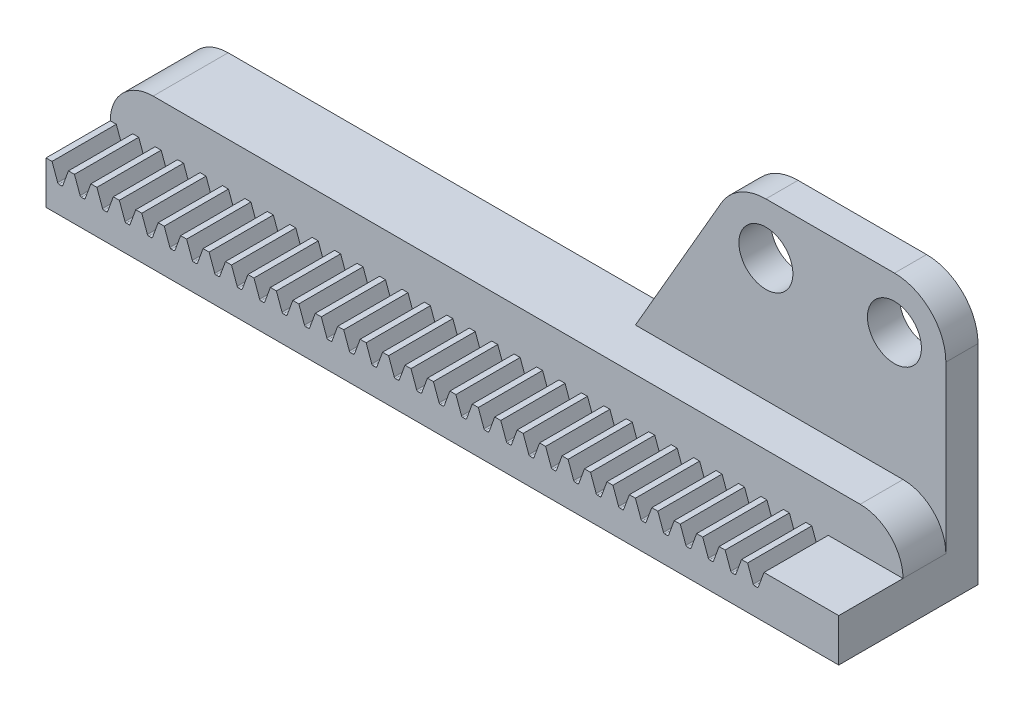
SolidWorks part; units mm, degrees
ref_plane "Front Plane" through (0, 0, 0) normal (0, 0, 1) x (1, 0, 0)
ref_plane "Top Plane" through (0, 0, 0) normal (0, 1, 0) x (1, 0, 0)
ref_plane "Right Plane" through (0, 0, 0) normal (1, 0, 0) x (0, 0, -1)
sketch "Sketch1" plane through (0, 0, 0) normal (0, 0, 1) x (1, 0, 0)
  line L0 (0, -1.5875) -> (-29.3687, -1.5875) construction
  line L1 (0, -1.5875) -> (29.3687, -1.5875) construction
  line L2 (0, -1.5875) -> (0, 1.5875) construction
  line L3 (-29.3687, 1.1811) -> (29.3687, 1.1811) construction
  line L4 (0, -1.5875) -> (3.0033, 6.664) construction
  point P3 (1189.8313, -1.5875)
  point P7 (0, 1.5875)
  dimension "Length" = 58.7375
  dimension "Gear Pitch" = 1219.2
  dimension "Height" = 3.175
  dimension "Pitch Height" = 2.7686
  dimension "Pressure Angle" = 20
sketch "Sketch2" plane through (0, 0, 0) normal (1, 0, 0) x (0, 0, -1)
  line L0 (2.3813, 0) -> (-2.3813, 0) construction
  point P3 (0, 0)
  dimension "Face Width" = 4.7625
sketch "Sketch3" plane through (0, 0, 0) normal (1, 0, 0) x (0, 0, -1)
  line L0 (0, -1.5875) -> (0, 1.5875) construction
  line L1 (2.3813, 1.5875) -> (-2.3813, 1.5875)
  line L2 (0, 0) -> (-2.3813, 0) construction
  line L3 (0, 0) -> (2.3813, 0) construction
  line L4 (-2.3813, 1.5875) -> (-2.3813, -1.5875)
  line L5 (-2.3813, -1.5875) -> (2.3813, -1.5875)
  line L6 (2.3813, -1.5875) -> (2.3813, 1.5875)
extrude "Boss-Extrude1" add sketch "Sketch3" along normal up to vertex (29.3687 mm away) and the other way up to vertex (29.3687 mm away) up to point (29.3687, -1.5875, 0) other way up to point (-29.3687, -1.5875, 0)
sketch "Sketch4" plane through (0, 0, 0) normal (0, 0, 1) x (1, 0, 0)
  line L0 (-28.9227, 1.5875) -> (-28.4805, 0.3725)
  line L2 (-28.4805, 0.3725) -> (-28.1485, 0.3725)
  line L3 (-28.1485, 0.3725) -> (-27.7063, 1.5875)
  line L4 (-28.9227, 1.5875) -> (-27.7063, 1.5875)
  line L5 (-28.9227, 1.5875) -> (-29.3687, 1.5875) construction
  line L6 (-27.7063, 1.5875) -> (-27.2603, 1.5875) construction
  line L7 (-27.2603, 1.5875) -> (-26.8181, 0.3725) construction
  line L8 (-28.3145, 0.3725) -> (-28.3145, 1.5875) construction
  line L9 (-28.7301, 1.0583) -> (-27.8989, 1.0583) construction
  line L10 (-27.8989, 1.0583) -> (-27.8989, 1.5875) construction
  line L11 (-27.0677, 1.0583) -> (-27.0677, 0.3725) construction
  line L12 (-27.8989, 1.0583) -> (-27.0677, 1.0583) construction
  line L13 (-29.3687, 1.5875) -> (-29.3687, -1.5875) construction
  line L14 (29.3687, 1.5875) -> (-29.3687, 1.5875) construction
  dimension "D1" = 20
  dimension "D2" = 20
  dimension "D3" = 1.215
  dimension "D4" = 0.5292
  dimension "D5" = 1.6624
  dimension "D6" = 0.332
  dimension "D7" = 0.446
extrude "Cut-Extrude1" cut sketch "Sketch4" against normal through all both and the other way through all
fillet "Fillet1" radius 0.0996 2 edges at (-28.1485, 0.3725, 0) (-28.4805, 0.3725, 0)
pattern_linear "LPattern1" count 32 spacing 1.6624 along (1, 0, 0) of "Cut-Extrude1", "Fillet1"
sketch "Sketch6" plane through (0, 0, 0) normal (0, 0, 1) x (1, 0, 0)
  line L0 (-24.049, 1.5875) -> (-24.049, -1.5875) construction
  line L1 (-23.9354, 1.5875) -> (-24.3815, 1.5875) construction
  line L2 (29.3687, -1.5875) -> (-29.3687, -1.5875) construction
  line L3 (24.049, 1.5875) -> (24.049, -1.5875) construction
  line L5 (24.049, 0) -> (29.3687, 0) construction
  line L6 (29.3687, 1.5875) -> (29.3687, -1.5875) construction
  line L7 (-24.049, 0) -> (-29.3687, 0) construction
  line L8 (-29.3687, 1.5875) -> (-29.3687, -1.5875) construction
  dimension "D1" = 5.3198
sketch "Sketch8" plane through (0, 0, -2.3813) normal (0, 0, -1) x (-1, 0, 0)
  line L0 (-29.3687, -1.5875) -> (-29.3687, 1.5875)
  line L3 (-26.1937, 4.7625) -> (26.1937, 4.7625)
  line L4 (29.3687, 1.5875) -> (29.3687, -1.5875)
  line L5 (29.3687, -1.5875) -> (-29.3687, -1.5875)
  arc A2 (26.1937, 4.7625) -> (29.3687, 1.5875) centre (26.1937, 1.5875) cw
  arc A5 (-29.3687, 1.5875) -> (-26.1937, 4.7625) centre (-26.1937, 1.5875) cw
  dimension "D1" = 3.175
  dimension "D2" = 6.35
extrude "Boss-Extrude2" add sketch "Sketch8" along normal blind 5.5562
sketch "Sketch9" plane through (0, 0, -7.9375) normal (0, 0, 1) x (1, 0, 0)
  line L5 (29.3687, -1.5875) -> (2.7035, -1.5875)
  line L9 (12.7342, 15.7861) -> (2.7035, -1.5875)
  line L10 (25.5587, 17.6911) -> (16.0337, 17.6911)
  line L11 (29.3687, -1.5875) -> (29.3687, 13.8811)
  circle A5 centre (16.0337, 13.8811) radius 2
  circle A6 centre (25.5587, 13.8811) radius 2
  arc A8 (16.0337, 17.6911) -> (12.7342, 15.7861) centre (16.0337, 13.8811) ccw
  arc A9 (29.3687, 13.8811) -> (25.5587, 17.6911) centre (25.5587, 13.8811) ccw
  dimension "D1" = 9.525
  dimension "D3" = 4
  dimension "D5" = 3.81
  dimension "D2" = 15.4686
  dimension "D4" = 60
extrude "Boss-Extrude3" add sketch "Sketch9" along normal blind 2.3813
equation "\"D3@Sketch4\" =  ( 2.2 / \"Gear Pitch@Sketch1\" )  + .002"
equation "\"D4@Sketch4\" = 1 / \"Gear Pitch@Sketch1\""
equation "\"D5@Sketch4\" = 3.1416 / \"Gear Pitch@Sketch1\""
equation "\"D1@Fillet1\" = \"D6@Sketch4\" * .3"
equation "\"D3@LPattern1\" = \"D5@Sketch4\""
equation "\"D1@Sketch4\"=\"Pressure Angle@Sketch1\""
equation "\"D2@Sketch4\"=\"Pressure Angle@Sketch1\""
equation "\"D1@Sketch6\"=(3.14159/\"Gear Pitch@Sketch1\")*3.2"
